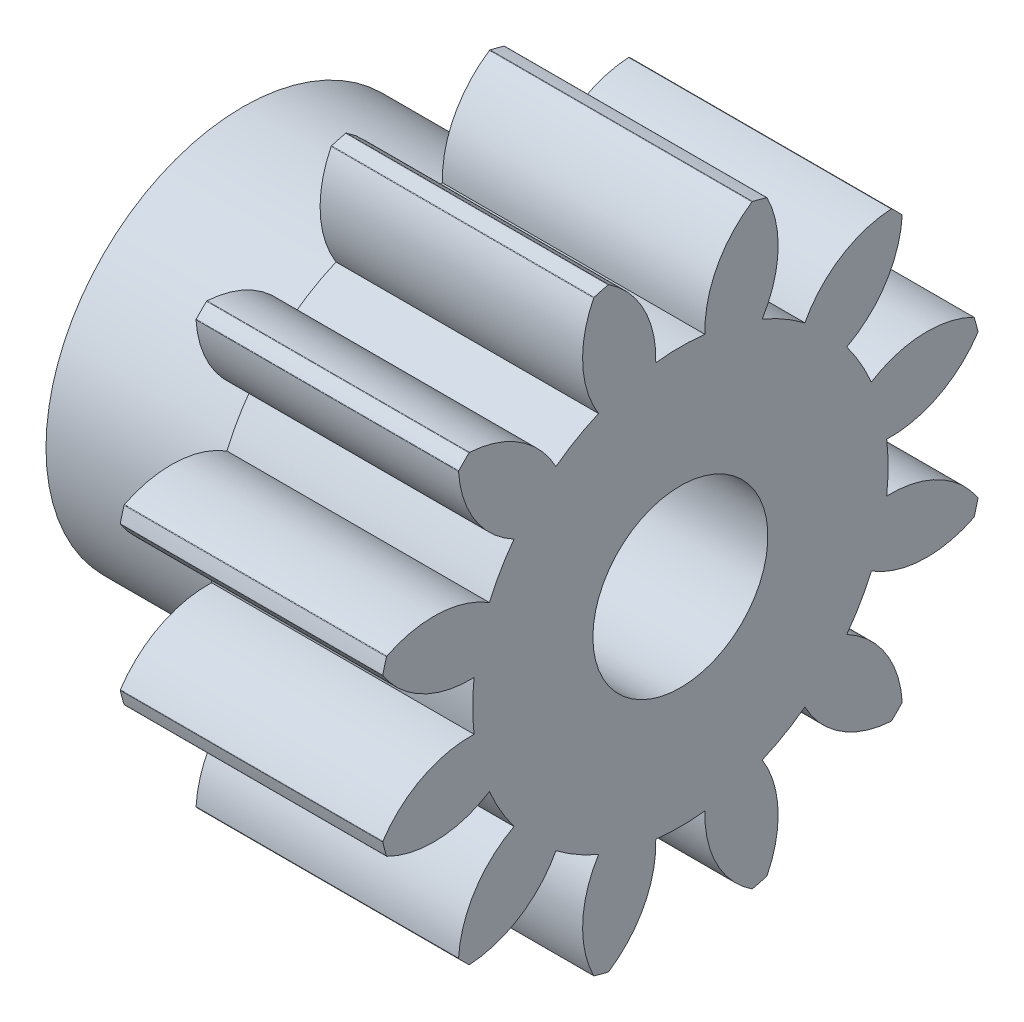
SolidWorks part; units mm, degrees
material "Nylon 101"
ref_plane "Plane1" through (0, 0, 0) normal (0, 0, 1) x (1, 0, 0)
ref_plane "Plane2" through (0, 0, 0) normal (0, 1, 0) x (1, 0, 0)
ref_plane "Plane3" through (0, 0, 0) normal (1, 0, 0) x (0, 0, -1)
sketch "HoldingSke" plane through (0, 0, 0) normal (0, 1, 0) x (1, 0, 0)
  line L0 (0, 0) -> (0.9781, -0.2079)
  line L1 (-15, 0) -> (100, 0) construction
  line L2 (0, 0) -> (-2.1039, 2.3779)
  line L3 (0, 0) -> (-11.863, 4.5341)
  line L4 (0, 0) -> (8.4473, 1.7955)
  line L5 (0, 0) -> (-46.8476, -17.4728)
  line L6 (0, 0) -> (-4.9738, -3.3558)
  line L7 (-2.1039, 2.3779) -> (8.6586, 51.2059)
  line L8 (-76.2, 54.61) -> (-75.5, 54.61)
  line L9 (-71.009, 38.7566) -> (-53.1078, 45.2721)
  line L10 (-76.2, 71.12) -> (104.1128, 71.12)
  line L11 (0, 0) -> (-6, 0)
  line L12 (-76.2, 101.6) -> (-76.162, 101.6)
  line L13 (24.9733, 27.94) -> (52.9518, 28.4284)
  line L14 (24.9733, 27.94) -> (24.9743, 27.94)
  line L15 (24.9733, 27.94) -> (100.4006, 29.5858)
  line L16 (-63.627, -1) -> (-12.827, -1)
  circle A0 centre (0, 0) radius 2
  circle A1 centre (0, 0) radius 4.749
  circle A2 centre (0, 0) radius 37.5
  circle A3 centre (0, 0) radius 2
  dimension "MHD" = 9.498
  dimension "Hub_dia" = 75
  dimension "Bore" = 4
  dimension "MBD" = 4
  dimension "Num_teeth" = 12
  dimension "Pitch" = 1
  dimension "Overall_len" = 50
  dimension "Show_teeth" = 12
  dimension "Thickness" = 6
  dimension "OAL" = 50.0001
  dimension "T_dim" = 0.7
  dimension "Ap" = 20
  dimension "H" = 19.05
  dimension "Pitch_radius" = 180.3128
  dimension "Width" = 6
  dimension "Backlash" = 0.038
  dimension "Addendum_fac" = 1
  dimension "Dedendum_fac" = 1.25
  dimension "Clearance_fac" = 0.25
  dimension "Dedendum_add" = 0.001
  dimension "Module" = 1
sketch "BasProSke" plane through (0, 0, 0) normal (0, 1, 0) x (1, 0, 0)
  line L0 (-10, 0) -> (60, 0) construction
  line L1 (0, 0) -> (0, 7)
  line L2 (0, 0) -> (6, 0)
  line L3 (6, 0) -> (6, 7)
  line L4 (6, 7) -> (0, 7)
  dimension "Thickness" = 6
  dimension "Diameter" = 14
revolve "Base-Revolve" add sketch "BasProSke" angle 360 about L0
sketch "TooCutSke" plane through (0, 0, 0) normal (1, 0, 0) x (0, 0, -1)
  line L1 (0, 0) -> (0, 107) construction
  line L2 (0, 0) -> (-0.8496, 5.9395) construction
  line L3 (0, 0) -> (-3.0836, 11.5081) construction
  line L4 (-0.8496, 5.9395) -> (-1.5418, 5.7541) construction
  arc A0 (0.5622, 4.7156) -> (-0.5622, 4.7156) centre (0, 0) ccw
  arc A1 (1.6729, 6.8233) -> (-1.6729, 6.8233) centre (0, 0) ccw
  circle A2 centre (0, 0) radius 6 construction
  circle A3 centre (0, 0) radius 5.6382 construction
  arc A4 (-0.5622, 4.7156) -> (-1.6729, 6.8233) centre (-2.9608, 4.7982) ccw
  arc A5 (1.6729, 6.8233) -> (0.5622, 4.7156) centre (2.9608, 4.7982) ccw
  dimension "Root_dia" = 9.498
  dimension "Overcut_dia" = 14.0508
  dimension "Pitch_dia" = 12
  dimension "Base_dia" = 11.2763
  dimension "Flank_rad" = 2.4
  dimension "Half_ang" = 15
  dimension "Half_CT" = 0.7167
extrude "ToothCut" cut sketch "TooCutSke" along normal through all
fillet "Breaks" radius 0.02 2 edges at (3, 6.8043, -1.6435) (3, 6.8043, 1.6435)
fillet "RootFillets" [suppressed] radius 0.251
pattern_circular "TeethCuts" count 12 over 360 about axis through (0, 0, 0) along (1, 0, 0) of "ToothCut", "Breaks", "RootFillets"
sketch "HubNeaOneSke" plane through (0, 0, 0) normal (-1, 0, 0) x (0, 0, 1)
  circle A0 centre (0, 0) radius 4.749
  dimension "Diameter" = 9.498
extrude "HubNearOne" [suppressed] add sketch "HubNeaOneSke" along normal blind 44.0001
sketch "HubNeaBotSke" plane through (0, 0, 0) normal (-1, 0, 0) x (0, 0, 1)
  circle A0 centre (0, 0) radius 4.749
  dimension "Diameter" = 9.498
extrude "HubNearBoth" [suppressed] add sketch "HubNeaBotSke" along normal blind 22
ref_plane "FarPln" through (6, 0, 0) normal (1, 0, 0) x (0, 0, -1)
sketch "HubFarSke" plane through (6, 0, 0) normal (1, 0, 0) x (0, 0, -1)
  circle A0 centre (0, 0) radius 4.749
  dimension "Diameter" = 9.498
extrude "HubFar" [suppressed] add sketch "HubFarSke" along normal blind 22
sketch "BorSke" plane through (0, 0, 0) normal (1, 0, 0) x (0, 0, -1)
  circle A0 centre (0, 0) radius 2
  dimension "Diameter" = 4
extrude "Bore" cut sketch "BorSke" along normal mid plane 100.0001
sketch "KeySke" plane through (0, 0, 0) normal (1, 0, 0) x (0, 0, -1)
  line L0 (-0.8, 0) -> (-0.8, 2.7)
  line L1 (-0.8, 2.7) -> (0.8, 2.7)
  line L2 (0.8, 2.7) -> (0.8, 0)
  line L3 (0, 0) -> (0, 34) construction
  line L4 (-0.8, 0) -> (0.8, 0)
  dimension "Offset" = 2.7
  dimension "Width" = 1.6
extrude "Keyway" [suppressed] cut sketch "KeySke" along normal mid plane 100.0001
pattern_circular "Keyway2" [suppressed] count 2 every 90 about axis through (-10, 0, 0) along (1, 0, 0)
ref_plane "Плоскость1" through (-4, 0, 0) normal (-1, 0, 0) x (0, 0, 1)
sketch "Эскиз3" plane through (-4, 0, 0) normal (-1, 0, 0) x (0, 0, 1)
  line L0 (0, 0) -> (-0.9356, 2.3183) construction
  line L1 (-0.7859, 1.9474) -> (-0.723, 2.3932)
  line L2 (-0.7859, 1.9474) -> (-1.1405, 2.2247)
  line L3 (-0.1456, 2.0949) -> (0.0519, 2.4995)
  line L4 (-0.1456, 2.0949) -> (-0.3972, 2.4682)
  line L5 (0, 0) -> (-0.1734, 2.494) construction
  line L6 (0.5089, 2.0374) -> (0.8217, 2.3611)
  line L7 (0.5089, 2.0374) -> (0.385, 2.4702)
  line L8 (0, 0) -> (0.6058, 2.4255) construction
  line L9 (1.1136, 1.7804) -> (1.5111, 1.9916)
  line L10 (1.1136, 1.7804) -> (1.1295, 2.2303)
  line L11 (0, 0) -> (1.3257, 2.1196) construction
  line L12 (1.6093, 1.3492) -> (2.0526, 1.4272)
  line L13 (1.6093, 1.3492) -> (1.7634, 1.7721)
  line L14 (0, 0) -> (1.9158, 1.6062) construction
  line L15 (1.9474, 0.7859) -> (2.3932, 0.723)
  line L16 (1.9474, 0.7859) -> (2.2247, 1.1405)
  line L17 (0, 0) -> (2.3183, 0.9356) construction
  line L18 (2.0949, 0.1456) -> (2.4995, -0.0519)
  line L19 (2.0949, 0.1456) -> (2.4682, 0.3972)
  line L20 (0, 0) -> (2.494, 0.1734) construction
  line L21 (2.0374, -0.5089) -> (2.3611, -0.8217)
  line L22 (2.0374, -0.5089) -> (2.4702, -0.385)
  line L23 (0, 0) -> (2.4255, -0.6058) construction
  line L24 (1.7804, -1.1136) -> (1.9916, -1.5111)
  line L25 (1.7804, -1.1136) -> (2.2303, -1.1295)
  line L26 (0, 0) -> (2.1196, -1.3257) construction
  line L27 (1.3492, -1.6093) -> (1.4272, -2.0526)
  line L28 (1.3492, -1.6093) -> (1.7721, -1.7634)
  line L29 (0, 0) -> (1.6062, -1.9158) construction
  line L30 (0.7859, -1.9474) -> (0.723, -2.3932)
  line L31 (0.7859, -1.9474) -> (1.1405, -2.2247)
  line L32 (0, 0) -> (0.9356, -2.3183) construction
  line L33 (0.1456, -2.0949) -> (-0.0519, -2.4995)
  line L34 (0.1456, -2.0949) -> (0.3972, -2.4682)
  line L35 (0, 0) -> (0.1734, -2.494) construction
  line L36 (-0.5089, -2.0374) -> (-0.8217, -2.3611)
  line L37 (-0.5089, -2.0374) -> (-0.385, -2.4702)
  line L38 (0, 0) -> (-0.6058, -2.4255) construction
  line L39 (-1.1136, -1.7804) -> (-1.5111, -1.9916)
  line L40 (-1.1136, -1.7804) -> (-1.1295, -2.2303)
  line L41 (0, 0) -> (-1.3257, -2.1196) construction
  line L42 (-1.6093, -1.3492) -> (-2.0526, -1.4272)
  line L43 (-1.6093, -1.3492) -> (-1.7634, -1.7721)
  line L44 (0, 0) -> (-1.9158, -1.6062) construction
  line L45 (-1.9474, -0.7859) -> (-2.3932, -0.723)
  line L46 (-1.9474, -0.7859) -> (-2.2247, -1.1405)
  line L47 (0, 0) -> (-2.3183, -0.9356) construction
  line L48 (-2.0949, -0.1456) -> (-2.4995, 0.0519)
  line L49 (-2.0949, -0.1456) -> (-2.4682, -0.3972)
  line L50 (0, 0) -> (-2.494, -0.1734) construction
  line L51 (-2.0374, 0.5089) -> (-2.3611, 0.8217)
  line L52 (-2.0374, 0.5089) -> (-2.4702, 0.385)
  line L53 (0, 0) -> (-2.4255, 0.6058) construction
  line L54 (-1.7804, 1.1136) -> (-1.9916, 1.5111)
  line L55 (-1.7804, 1.1136) -> (-2.2303, 1.1295)
  line L56 (0, 0) -> (-2.1196, 1.3257) construction
  line L57 (-1.3492, 1.6093) -> (-1.4272, 2.0526)
  line L58 (-1.3492, 1.6093) -> (-1.7721, 1.7634)
  line L59 (0, 0) -> (-1.6062, 1.9158) construction
  circle A0 centre (0, 0) radius 2.5
  circle A1 centre (0, 0) radius 2.1
  circle A2 centre (0, 0) radius 4.5
  circle A3 centre (0, 0) radius 2.2
  point P87 (0, 0)
  dimension "D1" = 5
  dimension "D2" = 4.2
  dimension "D4" = 9
  dimension "D6" = 4.4
  dimension "D3" = 30
  dimension "D5" = 20
extrude "Бобышка-Вытянуть2" add sketch "Эскиз3" against normal blind 4 separate body
sketch "Эскиз4" plane through (6, 0, 0) normal (1, 0, 0) x (0, 0, -1)
  circle A0 centre (0, 0) radius 2
equation "' \"Module@HoldingSke\" = 6.35"
equation "' \"Num_teeth@HoldingSke\" = 12"
equation "' \"Ap@HoldingSke\" =  20"
equation "' \"Ap@HoldingSke\" = 20"
equation "' \"Width@HoldingSke\" = 0.5 * 25.4"
equation "' \"Hub_dia@HoldingSke\"= 1 * 25.4"
equation "' \"Hub_dia@HoldingSke\" = 1 * 25.4"
equation "' \"Overall_len@HoldingSke\" = 1.0 * 25.4"
equation "' \"Bore@HoldingSke\" = 0.75 * 25.4"
equation "' \"T_dim@HoldingSke\" = 0.1 * 25.4"
equation "' \"Width@KeySke\" = 0.25 * 25.4"
equation "' \"Show_teeth@HoldingSke\" = 13"
equation "' \"Backlash@HoldingSke\" = 0.009 * 25.4"
equation "' \"Addendum_fac@HoldingSke\" = 1.0"
equation "' \"Dedendum_fac@HoldingSke\" = 1.25"
equation "' \"Dedendum_add@HoldingSke\" = 0.00005 * 25.4"
equation "' \"Clearance_fac@HoldingSke\" = 0.25"
equation "\"Pitch@HoldingSke\" = 1 / \"Module@HoldingSke\""
equation "\"Overcut_dia@TooCutSke\" = (\"Num_teeth@HoldingSke\" + 2 * \"Addendum_fac@HoldingSke\") / \"Pitch@HoldingSke\" + 0.002 * 25.4"
equation "\"Pitch_dia@TooCutSke\" = \"Num_teeth@HoldingSke\" / \"Pitch@HoldingSke\""
equation "\"Base_dia@TooCutSke\" = \"Num_teeth@HoldingSke\" / \"Pitch@HoldingSke\" * cos((\"Ap@HoldingSke\"  * 3.14159265 / 180))"
equation "\"Root_dia@TooCutSke\" = (\"Num_teeth@HoldingSke\" + 2) / \"Pitch@HoldingSke\" - 2 * (\"Addendum_fac@HoldingSke\" + \"Dedendum_fac@HoldingSke\") / \"Pitch@HoldingSke\" - \"Dedendum_add@HoldingSke\" * 2"
equation "\"Half_ang@TooCutSke\" = 180 / \"Num_teeth@HoldingSke\""
equation "\"Half_CT@TooCutSke\" = \"Num_teeth@HoldingSke\" / \"Pitch@HoldingSke\" * sin((3.14159265 / 2 / \"Num_teeth@HoldingSke\")) / 2 - 7 * \"Backlash@HoldingSke\" / 4"
equation "\"Flank_rad@TooCutSke\" = \"Num_teeth@HoldingSke\" / \"Pitch@HoldingSke\" / 5"
equation "\"Radius@RootFillets\" = \"Clearance_fac@HoldingSke\" / \"Pitch@HoldingSke\" + \"Dedendum_add@HoldingSke\""
equation "\"Break_rad@Breaks\" = 0.02 / \"Pitch@HoldingSke\""
equation "\"Thickness@HoldingSke\" = \"Width@HoldingSke\""
equation "\"OAL@HoldingSke\" = \"Thickness@HoldingSke\""
equation "\"MHD@HoldingSke\" = (\"Num_teeth@HoldingSke\" + 2) / \"Pitch@HoldingSke\" - 2 * (\"Addendum_fac@HoldingSke\" + \"Dedendum_fac@HoldingSke\")  / \"Pitch@HoldingSke\" - \"Dedendum_add@HoldingSke\" * 2"
equation "\"MBD@HoldingSke\" = (\"Num_teeth@HoldingSke\" + 2) / \"Pitch@HoldingSke\" - 2 * (\"Addendum_fac@HoldingSke\" + \"Dedendum_fac@HoldingSke\")  / \"Pitch@HoldingSke\" - \"Dedendum_add@HoldingSke\" * 2 - 0.002 * 25.4"
equation "\"MHD@HoldingSke\" = ((sgn( \"MHD@HoldingSke\" - \"Hub_dia@HoldingSke\" )-1)*( \"MHD@HoldingSke\" - \"Hub_dia@HoldingSke\" ))/-2+ \"Hub_dia@HoldingSke\""
equation "\"MBD@HoldingSke\" = ((sgn( \"MBD@HoldingSke\" - \"Bore@HoldingSke\" )-1)*( \"MBD@HoldingSke\" - \"Bore@HoldingSke\" ))/-2+ \"Bore@HoldingSke\""
equation "\"OAL@HoldingSke\" = ((sgn( \"OAL@HoldingSke\" - \"Overall_len@HoldingSke\" )+1)*( \"OAL@HoldingSke\" - \"Overall_len@HoldingSke\" ))/2 + \"Overall_len@HoldingSke\" + 0.000002 * 25.4"
equation "\"Num_teeth@TeethCuts\" = int( \"Show_teeth@HoldingSke\" ) + 1"
equation "\"Num_teeth@TeethCuts\" = ((sgn( \"Num_teeth@TeethCuts\" - \"Num_teeth@HoldingSke\" )-1)*( \"Num_teeth@TeethCuts\" - \"Num_teeth@HoldingSke\" ))/-2+ \"Num_teeth@HoldingSke\""
equation "\"Num_teeth@TeethCuts\" = ((sgn( \"Num_teeth@TeethCuts\" - 2.0)+1)*( \"Num_teeth@TeethCuts\" - 2.0))/2 +2.0"
equation "\"Angle@TeethCuts\" = 360.0 / \"Num_teeth@HoldingSke\""
equation "\"Diameter@BasProSke\" = (\"Num_teeth@HoldingSke\" + 2 * \"Addendum_fac@HoldingSke\") / \"Pitch@HoldingSke\""
equation "\"Thickness@BasProSke\"  = \"Thickness@HoldingSke\""
equation "' \"Fillet_rad@BasProSke\" =  \"Thickness@HoldingSke\" * 0.05"
equation "' \"Fillet_rad@BasProSke\" = \"Thickness@HoldingSke\" * 0.05"
equation "\"MHD@HoldingSke\" = ((sgn( \"MHD@HoldingSke\" - \"Root_dia@TooCutSke\" )-1)*( \"MHD@HoldingSke\" - \"Root_dia@TooCutSke\" ))/-2+ \"Root_dia@TooCutSke\""
equation "\"Diameter@HubNeaOneSke\" = \"MHD@HoldingSke\""
equation "\"Length@HubNearOne\" = \"OAL@HoldingSke\" - \"Thickness@BasProSke\""
equation "\"Diameter@HubNeaBotSke\" = \"MHD@HoldingSke\""
equation "\"Length@HubNearBoth\" = ( \"OAL@HoldingSke\" - \"Thickness@BasProSke\" ) / 2.0"
equation "\"Thickness@FarPln\" = \"Thickness@BasProSke\""
equation "\"Diameter@HubFarSke\" = \"MHD@HoldingSke\""
equation "\"Length@HubFar\" = ( \"OAL@HoldingSke\" - \"Thickness@BasProSke\" ) / 2.0"
equation "\"Diameter@BorSke\" = \"MBD@HoldingSke\""
equation "\"D1@Bore\" = \"OAL@HoldingSke\" * 2.0"
equation "\"D1@Keyway\" = \"OAL@HoldingSke\" * 2.0"
equation "\"Offset@KeySke\" = \"T_dim@HoldingSke\" + \"MBD@HoldingSke\" / 2.0"
